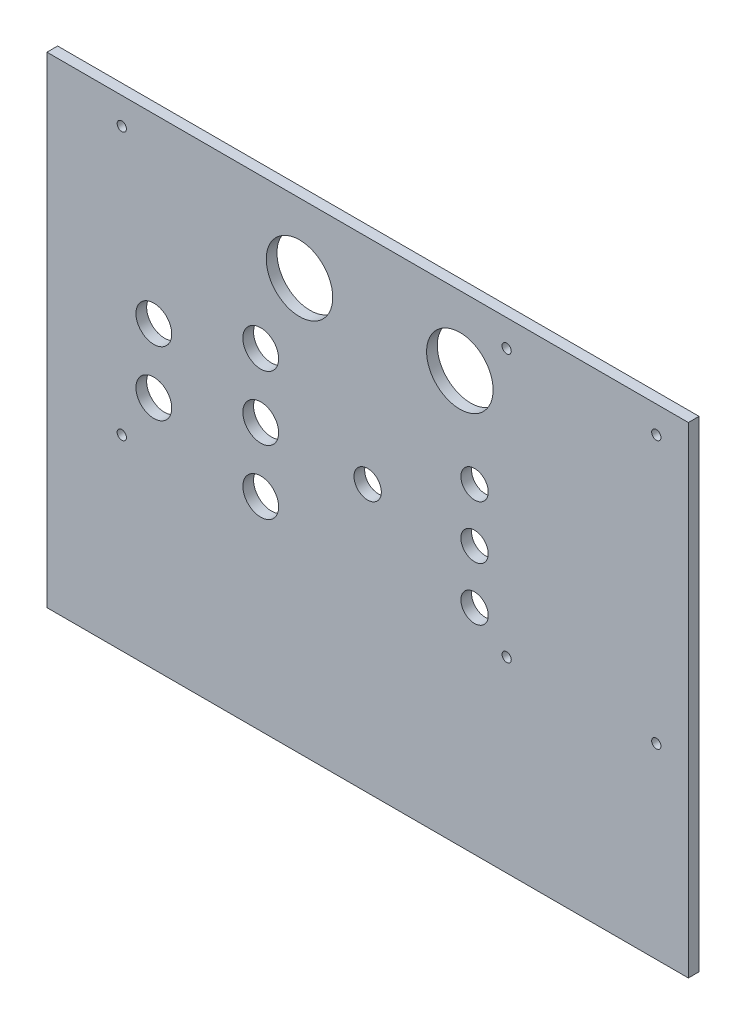
SolidWorks part; units mm, degrees
ref_plane "Front Plane" through (0, 0, 0) normal (0, 0, 1) x (1, 0, 0)
ref_plane "Top Plane" through (0, 0, 0) normal (0, 1, 0) x (1, 0, 0)
ref_plane "Right Plane" through (0, 0, 0) normal (1, 0, 0) x (0, 0, -1)
sketch "Sketch1" plane through (0, 0, 0) normal (0, 0, 1) x (1, 0, 0)
  line L0 (0, 0) -> (152.4, 0)
  line L1 (0, 0) -> (0, 114.3)
  line L2 (152.4, 0) -> (152.4, 114.3)
  line L3 (0, 114.3) -> (152.4, 114.3)
  line L4 (0, 38.1) -> (152.4, 38.1) construction
  line L5 (50.8, 63.5) -> (76.2, 63.5) construction
  line L6 (98.1072, 97.79) -> (60.0072, 97.79) construction
  line L7 (17.78, 107.95) -> (109.22, 107.95) construction
  circle A0 centre (60.0072, 97.79) radius 7.9
  circle A1 centre (98.1072, 97.79) radius 7.9
  circle A2 centre (60.0072, 97.79) radius 12 construction
  circle A3 centre (98.1072, 97.79) radius 12 construction
  circle A4 centre (25.4, 71.12) radius 4.25
  circle A5 centre (50.8, 78.74) radius 4.25
  circle A8 centre (25.4, 55.88) radius 4.25
  circle A9 centre (101.6, 76.2) radius 3.25
  circle A10 centre (101.6, 63.5) radius 3.25
  circle A11 centre (101.6, 50.8) radius 3.25
  circle A12 centre (50.8, 63.5) radius 4.25
  circle A13 centre (50.8, 48.26) radius 4.25
  circle A14 centre (76.2, 63.5) radius 3.25
  circle A15 centre (17.78, 44.45) radius 1.1
  circle A16 centre (17.78, 107.95) radius 1.1
  circle A17 centre (109.22, 107.95) radius 1.1
  circle A18 centre (109.22, 44.45) radius 1.1
  circle A19 centre (144.78, 44.45) radius 1.1
  circle A20 centre (144.78, 107.95) radius 1.1
  point P27 (29.594, 97.79)
  point P44 (96.2152, 97.79)
  point P45 (60.0072, 97.79)
  dimension "D4" = 15.8
  dimension "D5" = 15.8
  dimension "D6" = 24
  dimension "D7" = 8.5
  dimension "D8" = 6.5
  dimension "D9" = 15.24
  dimension "D18" = 25.4
  dimension "D19" = 25.4
  dimension "D20" = 2.2
  dimension "D21" = 11.43
  dimension "D1" = 152.4
  dimension "D2" = 114.3
  dimension "D3" = 38.1
  dimension "D10" = 15.24
  dimension "D11" = 25.4
  dimension "D12" = 7.62
  dimension "D13" = 15.24
  dimension "D14" = 12.7
  dimension "D15" = 12.7
  dimension "D16" = 25.4
  dimension "D17" = 25.4
  dimension "D22" = 36.83
  dimension "D23" = 7.62
  dimension "D24" = 35.56
  dimension "D25" = 7.62
  dimension "D26" = 10.16
  dimension "D27" = 38.1
extrude "Boss-Extrude1" add sketch "Sketch1" along normal blind 2.54
